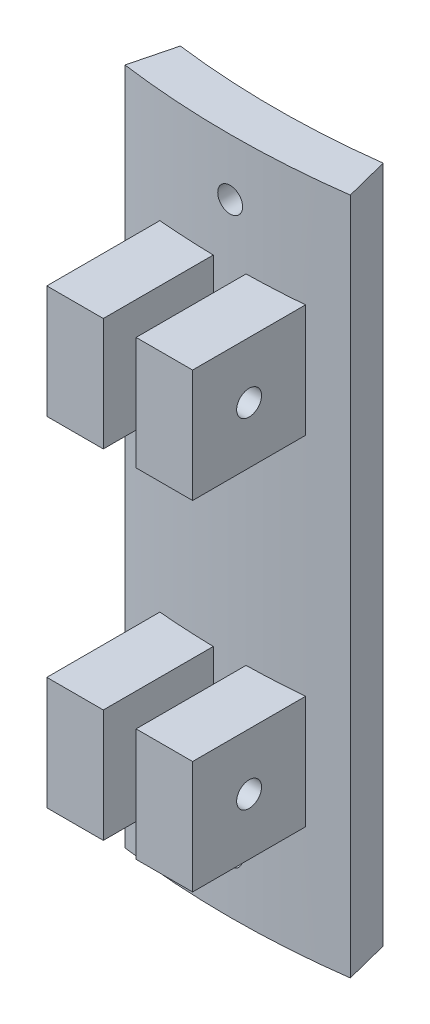
SolidWorks part; units mm, degrees
ref_plane "Front Plane" through (0, 0, 0) normal (0, 0, 1) x (1, 0, 0)
ref_plane "Top Plane" through (0, 0, 0) normal (0, 1, 0) x (1, 0, 0)
ref_plane "Right Plane" through (0, 0, 0) normal (1, 0, 0) x (0, 0, -1)
sketch "Sketch1" plane through (0, 0, 0) normal (0, 1, 0) x (1, 0, 0)
  line L0 (-8.255, -94.2542) -> (-8.255, -106.9542)
  line L1 (-8.255, -106.9542) -> (-1.905, -106.9542)
  line L2 (-1.905, -106.9542) -> (-1.905, -94.5958)
  line L3 (1.778, -94.5983) -> (1.778, -106.9542)
  line L4 (1.778, -106.9542) -> (8.128, -106.9542)
  line L5 (8.128, -106.9542) -> (8.128, -94.2652)
  line L6 (-11.399, -88.8064) -> (-12.6619, -93.7639)
  line L7 (11.399, -88.8064) -> (12.6619, -93.7639)
  line L8 (0, 0) -> (0, -106.9542) construction
  arc A0 (-12.6619, -93.7639) -> (-8.255, -94.2542) centre (0, 0) ccw
  arc A1 (-11.399, -88.8064) -> (11.399, -88.8064) centre (0, 0) ccw
  arc A2 (-1.905, -94.5958) -> (1.778, -94.5983) centre (0, 0) ccw
  arc A3 (8.128, -94.2652) -> (12.6619, -93.7639) centre (0, 0) ccw
  dimension "D1" = 94.615
  dimension "D2" = 89.535
  dimension "D4" = 22.86
  dimension "D5" = 25.4
  dimension "D3" = 3.683
  dimension "D6" = 6.35
  dimension "D7" = 1.905
  dimension "D8" = 12.7
extrude "Boss-Extrude1" add sketch "Sketch1" along normal blind 76.2
sketch "Sketch3" plane through (-8.255, 0, 0) normal (-1, 0, 0) x (0, 0, 1)
  line L0 (106.9542, 76.2) -> (106.9542, 0) construction
  line L1 (94.2542, 76.2) -> (106.9542, 76.2) construction
  circle A0 centre (100.6042, 57.15) radius 1.397
  circle A1 centre (100.6042, 19.05) radius 1.397
  point P8 (0, 0)
  dimension "D3" = 2.794
  dimension "D1" = 6.35
  dimension "D2" = 19.05
  dimension "D4" = 38.1
extrude "Cut-Extrude2" cut sketch "Sketch3" against normal blind 25.4
sketch "Sketch6" plane through (0, 0, 106.9542) normal (0, 0, 1) x (1, 0, 0)
  line L5 (-8.255, 76.2) -> (-8.255, 0) construction
  line L6 (-8.255, 25.4) -> (8.128, 25.4)
  line L7 (-8.255, 25.4) -> (-8.255, 50.8)
  line L8 (-8.255, 50.8) -> (8.128, 50.8)
  line L9 (8.128, 25.4) -> (8.128, 50.8)
  line L10 (8.128, 76.2) -> (8.128, 0) construction
  line L11 (-8.255, 63.5) -> (8.128, 63.5)
  line L12 (-8.255, 63.5) -> (-8.255, 76.2)
  line L13 (-8.255, 76.2) -> (8.128, 76.2)
  line L14 (8.128, 63.5) -> (8.128, 76.2)
  line L15 (-8.255, 0) -> (8.128, 0)
  line L16 (-8.255, 0) -> (-8.255, 12.7)
  line L17 (-8.255, 12.7) -> (8.128, 12.7)
  line L18 (8.128, 0) -> (8.128, 12.7)
  point P5 (8.128, 50.8)
  point P20 (0, 0)
  dimension "D1" = 12.7
  dimension "D2" = 12.7
  dimension "D3" = 12.7
  dimension "D4" = 12.7
extrude "Cut-Extrude4" cut sketch "Sketch6" against normal up to surface (12.7 mm away)
sketch "Sketch7" plane through (0, 0, 106.9542) normal (0, 0, 1) x (1, 0, 0)
  line L0 (-12.6619, 0) -> (12.6619, 0) construction
  circle A0 centre (0, 69.85) radius 1.397
  circle A1 centre (0, 6.35) radius 1.397
  point P4 (0, 0)
  point P7 (0, 0)
  point P8 (0, 0)
  point P12 (0, 0)
  dimension "D1" = 2.794
  dimension "D3" = 63.5
  dimension "D2" = 6.35
extrude "Cut-Extrude5" cut sketch "Sketch7" against normal blind 50.8
